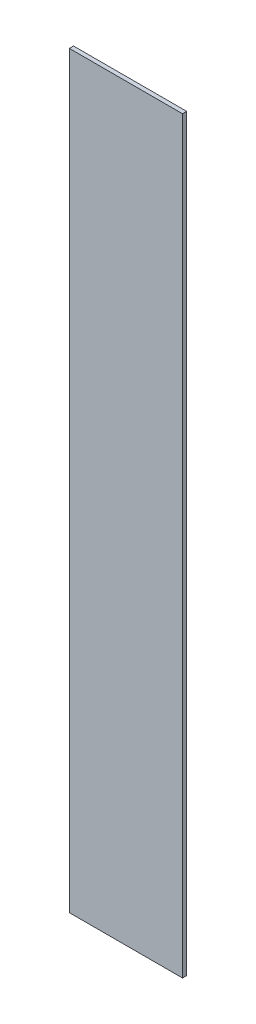
SolidWorks part; units mm, degrees
material "Acrylic (Medium-high impact)"
ref_plane "Front Plane" through (0, 0, 0) normal (0, 0, 1) x (1, 0, 0)
ref_plane "Top Plane" through (0, 0, 0) normal (0, 1, 0) x (1, 0, 0)
ref_plane "Right Plane" through (0, 0, 0) normal (1, 0, 0) x (0, 0, -1)
sketch "Sketch1" plane through (0, 0, 0) normal (0, 0, 1) x (1, 0, 0)
  line L1 (0, 0) -> (86.36, 0)
  line L2 (0, 0) -> (0, 571.5)
  line L3 (0, 571.5) -> (86.36, 571.5)
  line L4 (86.36, 0) -> (86.36, 571.5)
  dimension "D1" = 571.5
  dimension "D2" = 86.36
extrude "Boss-Extrude1" add sketch "Sketch1" along normal blind 3.175
